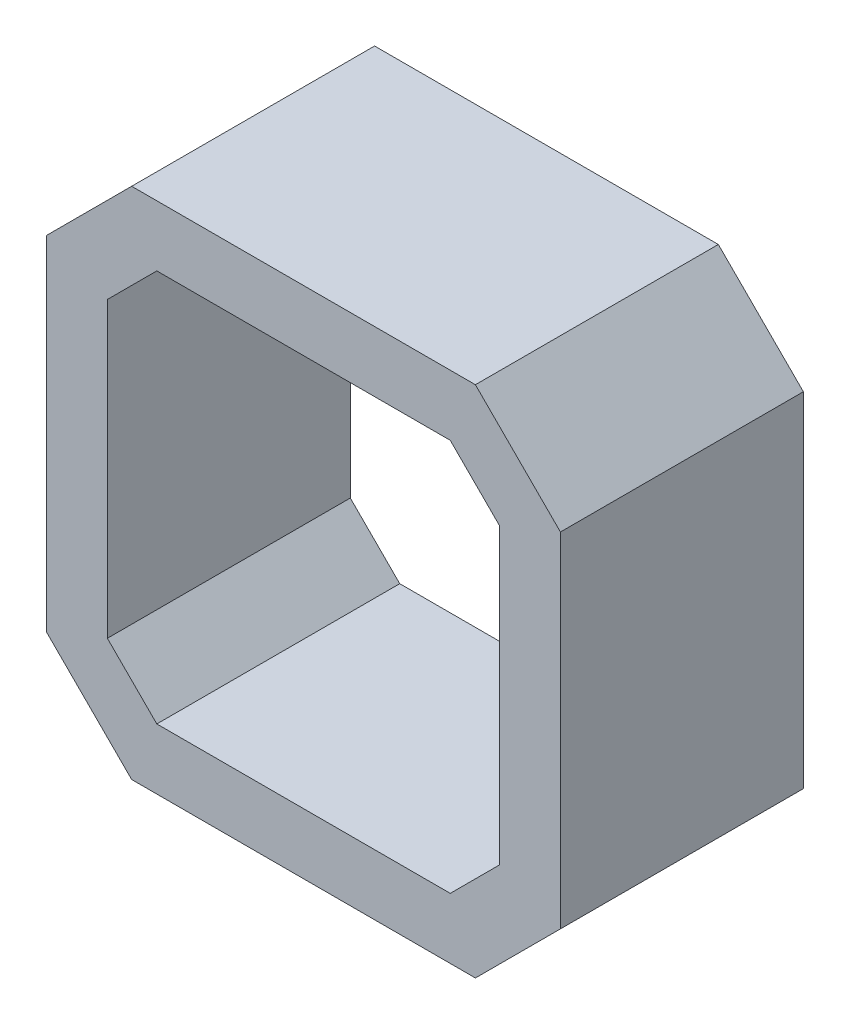
SolidWorks part; units mm, degrees
material "Ghisa grigia"
ref_plane "Piano frontale" through (0, 0, 0) normal (0, 0, 1) x (1, 0, 0)
ref_plane "Piano superiore" through (0, 0, 0) normal (0, 1, 0) x (1, 0, 0)
ref_plane "Piano destro" through (0, 0, 0) normal (1, 0, 0) x (0, 0, -1)
sketch "Schizzo1" plane through (0, 0, 0) normal (0, 0, 1) x (1, 0, 0)
  line L0 (-21.15, 14.15) -> (-14.15, 21.15)
  line L1 (-14.15, -21.15) -> (14.15, -21.15)
  line L2 (-21.15, -14.15) -> (-21.15, 14.15)
  line L3 (-14.15, 21.15) -> (14.15, 21.15)
  line L4 (21.15, -14.15) -> (21.15, 14.15)
  line L5 (-21.15, -21.15) -> (21.15, 21.15) construction
  line L6 (-21.15, 21.15) -> (21.15, -21.15) construction
  line L7 (14.15, 21.15) -> (21.15, 14.15)
  line L8 (14.15, -21.15) -> (21.15, -14.15)
  line L9 (-21.15, -14.15) -> (-14.15, -21.15)
  line L10 (-12.0789, 16.15) -> (12.0789, 16.15)
  line L11 (12.0789, 16.15) -> (16.15, 12.0789)
  line L12 (16.15, -12.0789) -> (16.15, 12.0789)
  line L13 (12.0789, -16.15) -> (16.15, -12.0789)
  line L14 (-12.0789, -16.15) -> (12.0789, -16.15)
  line L15 (-16.15, -12.0789) -> (-12.0789, -16.15)
  line L16 (-16.15, -12.0789) -> (-16.15, 12.0789)
  line L17 (-16.15, 12.0789) -> (-12.0789, 16.15)
  point P0 (0, 0)
  dimension "D1" = 42.3
  dimension "D2" = 42.3
  dimension "D3" = 5
extrude "Estrusione-Estrusione1" add sketch "Schizzo1" along normal blind 20
